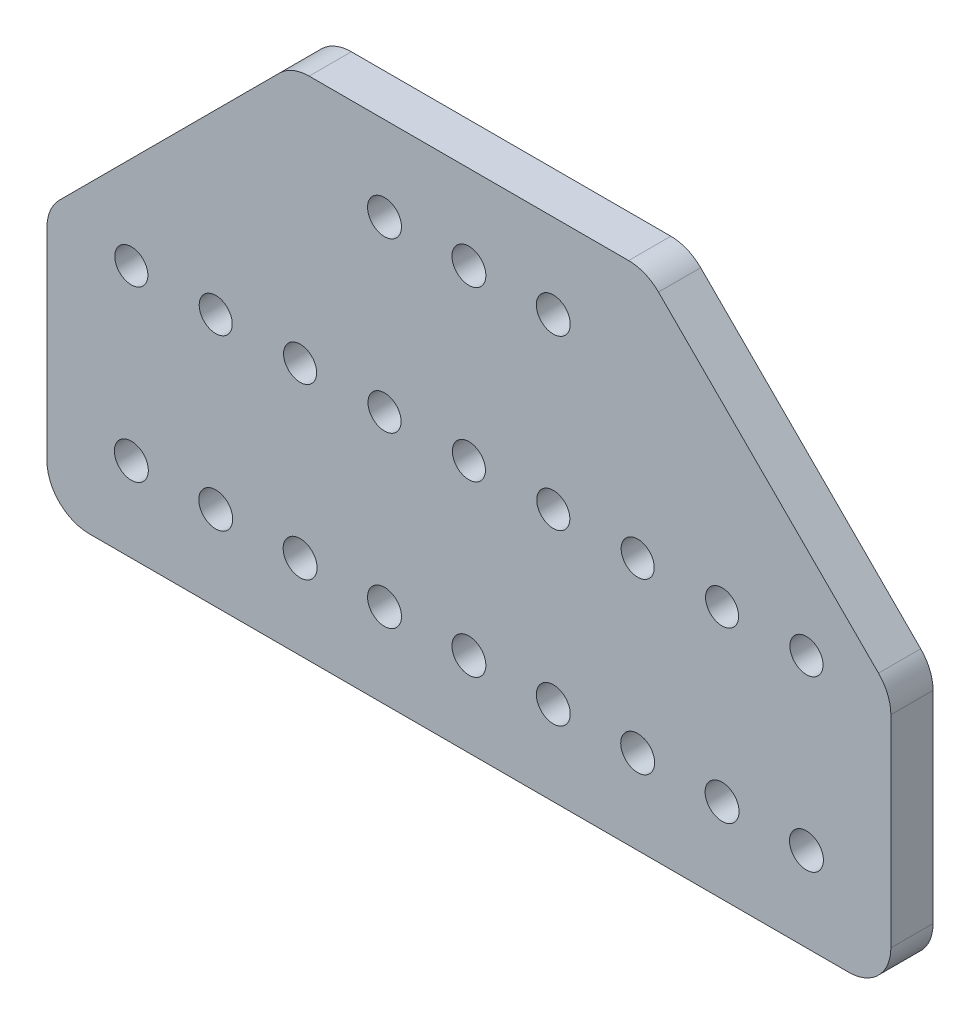
SolidWorks part; units mm, degrees
material "6061-T6 (SS)"
ref_plane "Front Plane" through (0, 0, 0) normal (0, 0, 1) x (1, 0, 0)
ref_plane "Top Plane" through (0, 0, 0) normal (0, 1, 0) x (1, 0, 0)
ref_plane "Right Plane" through (0, 0, 0) normal (1, 0, 0) x (0, 0, -1)
sketch "Sketch1" plane through (0, 0, 0) normal (0, 0, 1) x (1, 0, 0)
  line L1 (0, 0) -> (127, 0)
  line L2 (0, 0) -> (0, 82.55)
  line L3 (0, 82.55) -> (127, 82.55)
  line L4 (127, 0) -> (127, 82.55)
  dimension "D1" = 82.55
  dimension "D2" = 127
extrude "Boss-Extrude1" add sketch "Sketch1" along normal blind 6.35
sketch "Sketch2" plane through (0, 0, 0) normal (0, 0, -1) x (-1, 0, 0)
  line L0 (-127, 82.55) -> (0, 82.55) construction
  line L1 (0, 82.55) -> (0, 0) construction
  circle A0 centre (-76.2, 63.5) radius 2.5527
  circle A1 centre (-63.5, 63.5) radius 2.5527
  circle A2 centre (-50.8, 63.5) radius 2.5527
  dimension "D2" = 12.7
  dimension "D3" = 12.7
  dimension "D4" = 50.8
  dimension "D5" = 19.05
  dimension "D7" = 5.1054
  dimension "D8" = 5.1054
  dimension "D9" = 5.1054
extrude "Cut-Extrude1" cut sketch "Sketch2" against normal through all and the other way through all
sketch "Sketch3" plane through (0, 0, 0) normal (0, 0, -1) x (-1, 0, 0)
  line L0 (-127, 0) -> (-127, 82.55) construction
  line L1 (0, 0) -> (-127, 0) construction
  circle A0 centre (-114.3, 38.1) radius 2.4892
  circle A1 centre (-114.3, 25.4) radius 2.5527 construction
  circle A2 centre (-114.3, 12.7) radius 2.5527
  circle A3 centre (-101.6, 38.1) radius 2.4892
  circle A4 centre (-101.6, 25.4) radius 2.5527 construction
  circle A5 centre (-101.6, 12.7) radius 2.5527
  circle A6 centre (-88.9, 38.1) radius 2.4892
  circle A7 centre (-88.9, 25.4) radius 2.5527 construction
  circle A8 centre (-88.9, 12.7) radius 2.5527
  circle A9 centre (-76.2, 38.1) radius 2.4892
  circle A10 centre (-76.2, 25.4) radius 2.5527 construction
  circle A11 centre (-76.2, 12.7) radius 2.5527
  circle A12 centre (-63.5, 38.1) radius 2.4892
  circle A13 centre (-63.5, 25.4) radius 2.5527 construction
  circle A14 centre (-63.5, 12.7) radius 2.5527
  circle A15 centre (-50.8, 38.1) radius 2.4892
  circle A16 centre (-50.8, 25.4) radius 2.5527 construction
  circle A17 centre (-50.8, 12.7) radius 2.5527
  circle A18 centre (-38.1, 38.1) radius 2.4892
  circle A19 centre (-38.1, 25.4) radius 2.5527 construction
  circle A20 centre (-38.1, 12.7) radius 2.5527
  circle A21 centre (-25.4, 38.1) radius 2.4892
  circle A22 centre (-25.4, 25.4) radius 2.5527 construction
  circle A23 centre (-25.4, 12.7) radius 2.5527
  circle A24 centre (-12.7, 38.1) radius 2.4892
  circle A25 centre (-12.7, 25.4) radius 2.5527 construction
  circle A26 centre (-12.7, 12.7) radius 2.5527
  dimension "D1" = 4.9784
  dimension "D2" = 5.1054
  dimension "D3" = 5.1054
  dimension "D4" = 12.7
  dimension "D5" = 12.7
  dimension "D6" = 12.7
  dimension "D7" = 12.7
  dimension "D8" = 12.7
  dimension "D9" = 12.7
  dimension "D11" = 12.7
  dimension "D10" = 9
extrude "Cut-Extrude2" cut sketch "Sketch3" against normal through all
sketch "Sketch4" plane through (0, 0, 0) normal (0, 0, -1) x (-1, 0, 0)
  line L0 (-83.82, 82.55) -> (-127, 39.37)
  line L1 (-127, 82.55) -> (0, 82.55) construction
  line L2 (-127, 39.37) -> (-127, 82.55)
  line L3 (-127, 82.55) -> (-83.82, 82.55)
  line L4 (-43.18, 82.55) -> (0, 82.55)
  line L5 (0, 82.55) -> (0, 39.37)
  line L6 (0, 82.55) -> (0, 0) construction
  line L7 (0, 39.37) -> (-43.18, 82.55)
  dimension "D1" = 45
  dimension "D2" = 45
  dimension "D3" = 43.18
  dimension "D4" = 43.18
extrude "Cut-Extrude3" cut sketch "Sketch4" against normal through all
sketch "Sketch5" plane through (0, 0, 0) normal (0, 0, -1) x (-1, 0, 0)
  line L0 (-90.17, 76.2) -> (-36.83, 76.2)
  line L1 (-127, 39.37) -> (-83.82, 82.55) construction
  line L2 (-43.18, 82.55) -> (0, 39.37) construction
  line L3 (-36.83, 76.2) -> (-43.18, 82.55)
  line L4 (-43.18, 82.55) -> (-83.82, 82.55)
  line L5 (-83.82, 82.55) -> (-90.17, 76.2)
  dimension "D1" = 6.35
extrude "Cut-Extrude4" cut sketch "Sketch5" against normal through all
fillet "Fillet1" radius 6.35 6 edges at (127, 39.37, 3.175) (127, 0, 3.175) (0, 0, 3.175) (36.83, 76.2, 3.175) (90.17, 76.2, 3.175) (0, 39.37, 3.175)
